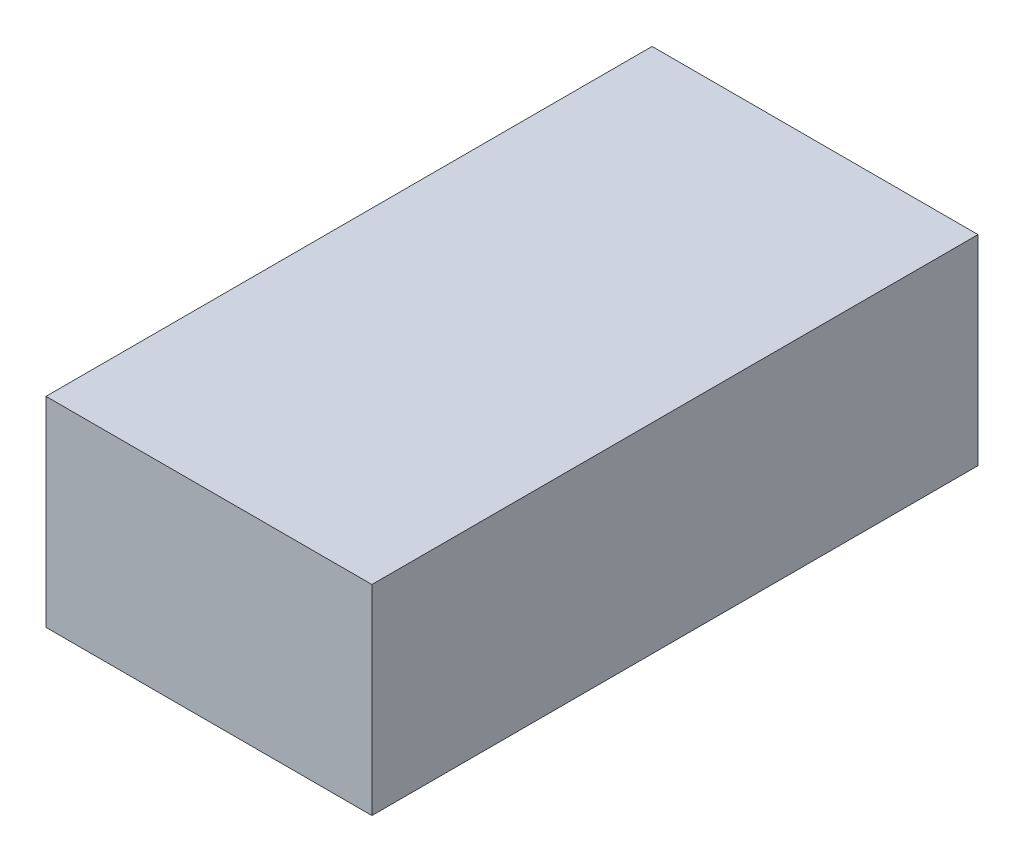
SolidWorks part; units mm, degrees
ref_plane "Front Plane" through (0, 0, 0) normal (0, 0, 1) x (1, 0, 0)
ref_plane "Top Plane" through (0, 0, 0) normal (0, 1, 0) x (1, 0, 0)
ref_plane "Right Plane" through (0, 0, 0) normal (1, 0, 0) x (0, 0, -1)
sketch "Sketch1" plane through (0, 0, 0) normal (0, 1, 0) x (1, 0, 0)
  line L1 (0, 0) -> (-57, 0)
  line L2 (0, 0) -> (0, -106)
  line L3 (0, -106) -> (-57, -106)
  line L4 (-57, 0) -> (-57, -106)
  dimension "D1" = 57
  dimension "D2" = 106
extrude "Boss-Extrude1" add sketch "Sketch1" along normal blind 35
